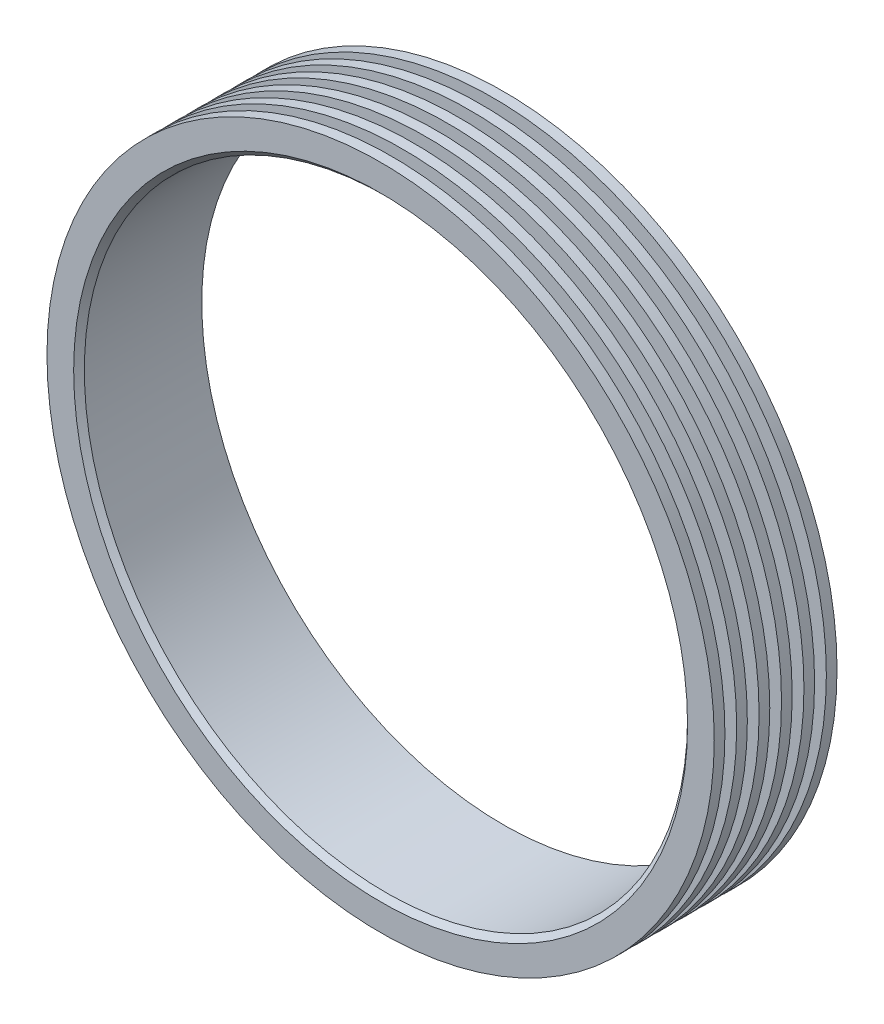
SolidWorks part; units mm, degrees
ref_plane "Piano frontale" through (0, 0, 0) normal (0, 0, 1) x (1, 0, 0)
ref_plane "Piano superiore" through (0, 0, 0) normal (0, 1, 0) x (1, 0, 0)
ref_plane "Piano destro" through (0, 0, 0) normal (1, 0, 0) x (0, 0, -1)
sketch "Schizzo1" plane through (0, 0, 0) normal (0, 0, 1) x (1, 0, 0)
  circle A0 centre (0, 0) radius 62.5
  circle A1 centre (0, 0) radius 56.5
sketch "Schizzo2" plane through (0, 0, 0) normal (1, 0, 0) x (0, 0, -1)
  line L0 (0, 56.5) -> (-10.5, 56.5)
  line L2 (11.5, 62.5) -> (9.5, 62.5)
  line L3 (7.3, 62.5) -> (5.3, 62.5)
  line L4 (3.1, 62.5) -> (1.1, 62.5)
  line L5 (-1.1, 62.5) -> (-3.1, 62.5)
  line L6 (-5.3, 62.5) -> (-7.3, 62.5)
  line L7 (-9.5, 62.5) -> (-11.5, 62.5)
  line L8 (11.5, 62.5) -> (7.3, 62.5) construction
  line L9 (-9.5, 62.5) -> (-9.5, 58.5)
  line L10 (-7.3, 62.5) -> (-7.3, 58.5)
  line L11 (-11.5, 57.5) -> (-11.5, 62.5)
  line L12 (-7.3, 58.5) -> (-9.5, 58.5)
  line L13 (-5.3, 62.5) -> (-5.3, 58.5)
  line L14 (-3.1, 58.5) -> (-5.3, 58.5)
  line L15 (-3.1, 62.5) -> (-3.1, 58.5)
  line L16 (1.1, 58.5) -> (-1.1, 58.5)
  line L17 (-1.1, 62.5) -> (-1.1, 58.5)
  line L18 (1.1, 62.5) -> (1.1, 58.5)
  line L19 (3.1, 62.5) -> (3.1, 58.5)
  line L20 (5.3, 62.5) -> (5.3, 58.5)
  line L21 (5.3, 58.5) -> (3.1, 58.5)
  line L22 (9.5, 62.5) -> (9.5, 58.5)
  line L23 (9.5, 58.5) -> (7.3, 58.5)
  line L24 (7.3, 62.5) -> (7.3, 58.5)
  line L25 (-10.5, 56.5) -> (-11.5, 57.5)
  line L27 (0, 0) -> (15.4663, 0) construction
  line L29 (0, 56.5) -> (11.5, 56.5)
  line L30 (11.5, 56.5) -> (11.5, 62.5)
  point P22 (-11.5, 56.5)
  dimension "D1" = 6
  dimension "D2" = 4.2
revolve "Rivoluzione1" add sketch "Schizzo2" angle 360 about L27
